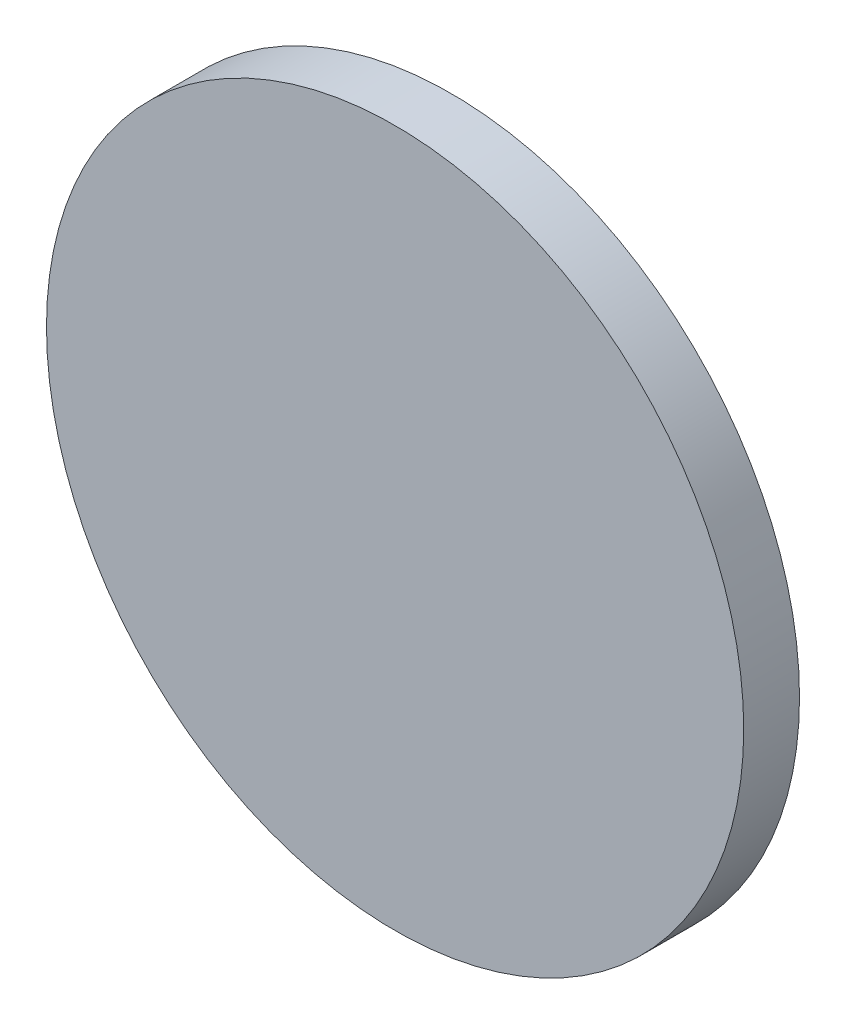
SolidWorks part; units mm, degrees
ref_plane "前视基准面" through (0, 0, 0) normal (0, 0, 1) x (1, 0, 0)
ref_plane "上视基准面" through (0, 0, 0) normal (0, 1, 0) x (1, 0, 0)
ref_plane "右视基准面" through (0, 0, 0) normal (1, 0, 0) x (0, 0, -1)
sketch "草图1" plane through (0, 0, 0) normal (0, 0, 1) x (1, 0, 0)
  circle A0 centre (0, 0) radius 12.5
extrude "凸台-拉伸1" add sketch "草图1" along normal blind 2
